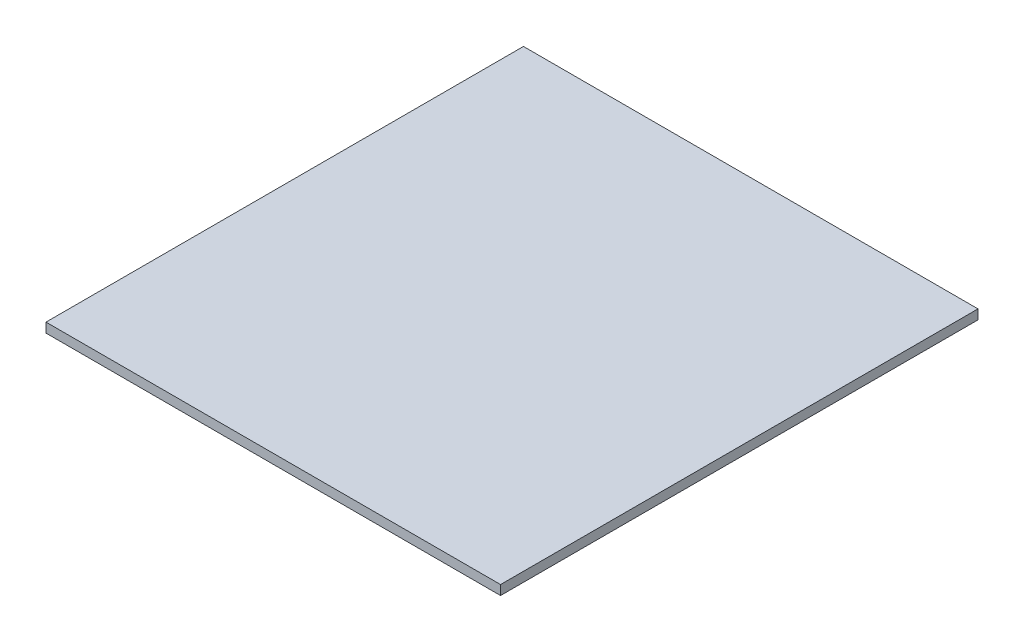
SolidWorks part; units mm, degrees
ref_plane "Спереди" through (0, 0, 0) normal (0, 0, 1) x (1, 0, 0)
ref_plane "Сверху" through (0, 0, 0) normal (0, 1, 0) x (1, 0, 0)
ref_plane "Справа" through (0, 0, 0) normal (1, 0, 0) x (0, 0, -1)
sketch "Эскиз1" plane through (0, 0, 0) normal (0, 1, 0) x (1, 0, 0)
  line L1 (0, 0) -> (238, 0)
  line L2 (0, 0) -> (0, 250)
  line L3 (0, 250) -> (238, 250)
  line L4 (238, 0) -> (238, 250)
extrude "Бобышка-Вытянуть1" add sketch "Эскиз1" along normal blind 5
